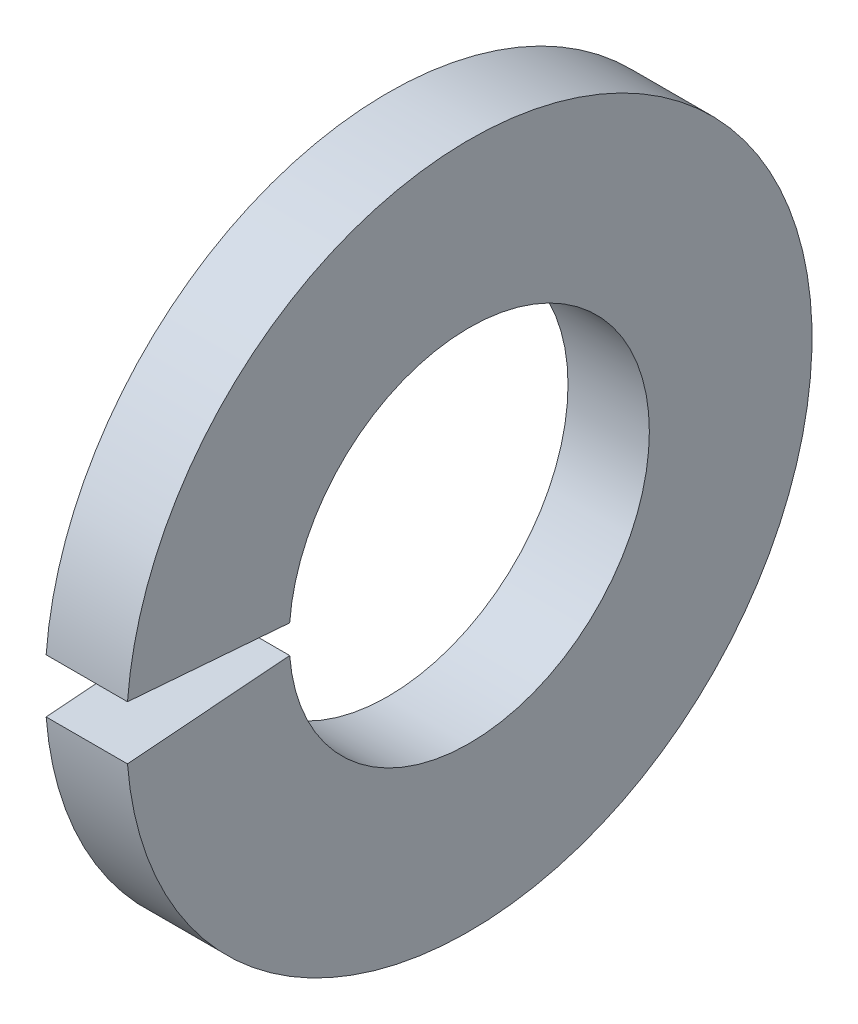
SolidWorks part; units mm, degrees
ref_plane "Plane1" through (0, 0, 0) normal (0, 0, 1) x (1, 0, 0)
ref_plane "Plane2" through (0, 0, 0) normal (0, 1, 0) x (1, 0, 0)
ref_plane "Plane3" through (0, 0, 0) normal (1, 0, 0) x (0, 0, -1)
sketch "Sketch1" plane through (0, 0, 0) normal (0, 0, 1) x (1, 0, 0)
  line L0 (-34.925, 0) -> (9.525, 0) construction
  line L1 (0, 1.55) -> (0, 2.95)
  line L2 (0, 2.95) -> (-0.7, 2.95)
  line L3 (-0.7, 2.95) -> (-0.7, 1.55)
  line L4 (-0.7, 1.55) -> (0, 1.55)
  dimension "Thickness" = 0.7
  dimension "Inside_dia" = 3.1
  dimension "Outside_dia" = 5.9
revolve "Base-Revolve" add sketch "Sketch1" angle 360 about L0
sketch "Sketch2" plane through (0, 0, 0) normal (-1, 0, 0) x (0, -1, 0)
  line L0 (0, 0) -> (0.2361, 2.9997)
  line L1 (0, -3.175) -> (0, 12.7) construction
  line L2 (0, 0) -> (-0.2361, 2.9997)
  arc A0 (0.2361, 2.9997) -> (-0.2361, 2.9997) centre (0, 0) ccw
  dimension "D1" = 3.009
  dimension "Gap_ang" = 9
extrude "Gap" cut sketch "Sketch2" along normal through all
equation "\"D1@Sketch2\" = \"Outside_dia@Sketch1\" * 0.51"
